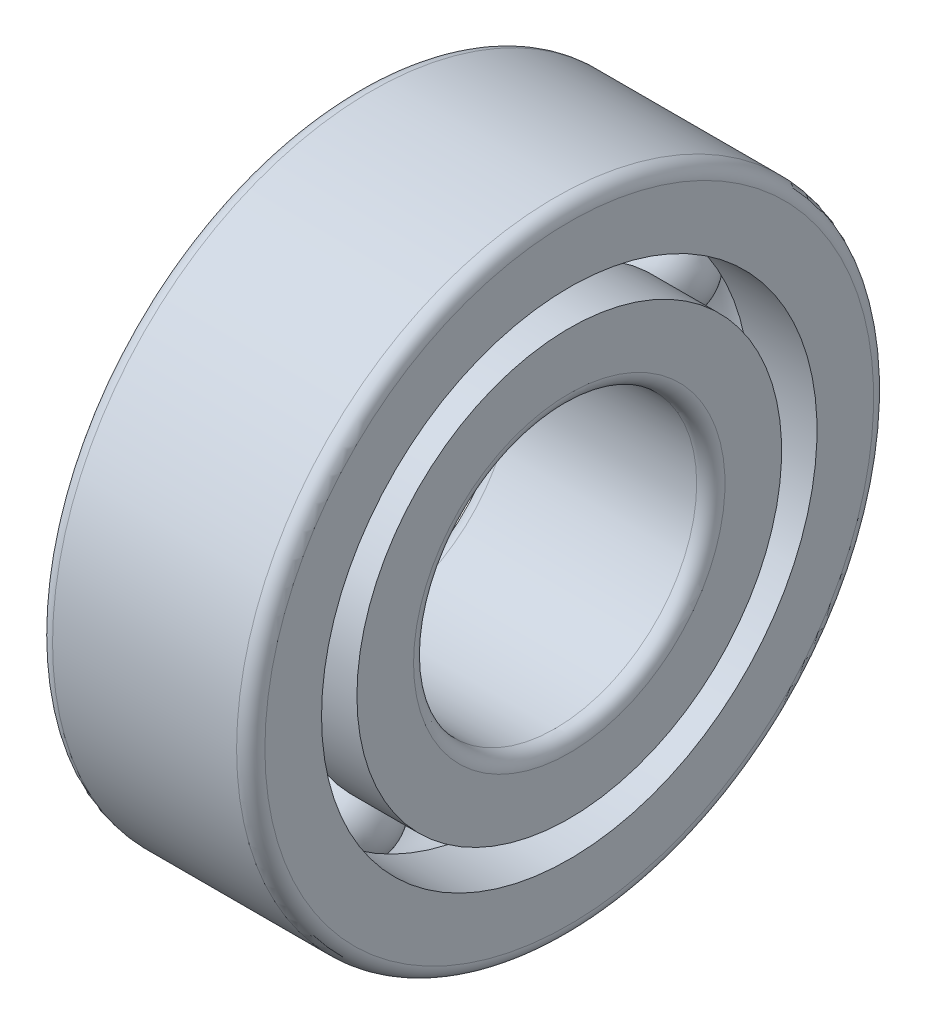
SolidWorks part; units mm, degrees
ref_plane "Front Plane" through (0, 0, 0) normal (0, 0, 1) x (1, 0, 0)
ref_plane "Top Plane" through (0, 0, 0) normal (0, 1, 0) x (1, 0, 0)
ref_plane "Right Plane" through (0, 0, 0) normal (1, 0, 0) x (0, 0, -1)
sketch "Sketch1" plane through (0, 0, 0) normal (0, 0, 1) x (1, 0, 0)
  line L0 (0, 22.5) -> (15, 22.5) construction
  line L1 (0, 0) -> (15, 0)
  line L3 (0, 45) -> (15, 45)
  line L5 (0, 32.5) -> (15, 32.5)
  line L6 (0, 12.5) -> (15, 12.5)
  line L7 (0, 7.5) -> (4.7728, 7.5)
  line L8 (0, 6.25) -> (15, 6.25) construction
  line L9 (0, 5) -> (4.7728, 5)
  line L10 (10.2272, 7.5) -> (15, 7.5)
  line L11 (10.2272, 5) -> (15, 5)
  line L16 (15, 45) -> (15, 0)
  line L17 (0, 45) -> (0, 0)
  arc A0 (4.7728, 5) -> (10.2272, 5) centre (7.5, 6.25) ccw
  arc A1 (10.2272, 7.5) -> (4.7728, 7.5) centre (7.5, 6.25) ccw
  dimension "D6" = 6
  dimension "D1" = 45
  dimension "D2" = 15
  dimension "D3" = 10
  dimension "D4" = 10
  dimension "D5" = 12.5
  dimension "D7" = 1.25
  dimension "D8" = 1.25
  dimension "D9" = 6.25
revolve "Revolve3" add sketch "Sketch1" angle 360 about L0
fillet "Fillet1" radius 1 2 edges at (0, 22.5, 22.5) (15, 22.5, 22.5)
fillet "Fillet2" radius 1 2 edges at (15, 22.5, 10) (0, 22.5, 10)
ref_plane "Plane1" through (0, 22.5, 0) normal (0, 1, 0) x (1, 0, 0)
sketch "Sketch5" plane through (0, 22.5, 0) normal (0, 1, 0) x (1, 0, 0)
  line L4 (14, 0) -> (1, 0)
  line L5 (14, 16.25) -> (1, 16.25)
  line L6 (10.5, 16.25) -> (4.5, 16.25)
  line L7 (14, 0) -> (1, 0)
  arc A0 (10.5, 16.25) -> (4.5, 16.25) centre (7.5, 16.25) ccw
  dimension "D1" = 22.5
  dimension "D2" = 6.25
revolve "Revolve4" add sketch "Sketch5" angle 360 about L6
pattern_circular "CirPattern2" count 12 over 360 about axis through (0, 22.5, 0) along (1, 0, 0) of bodies 109
